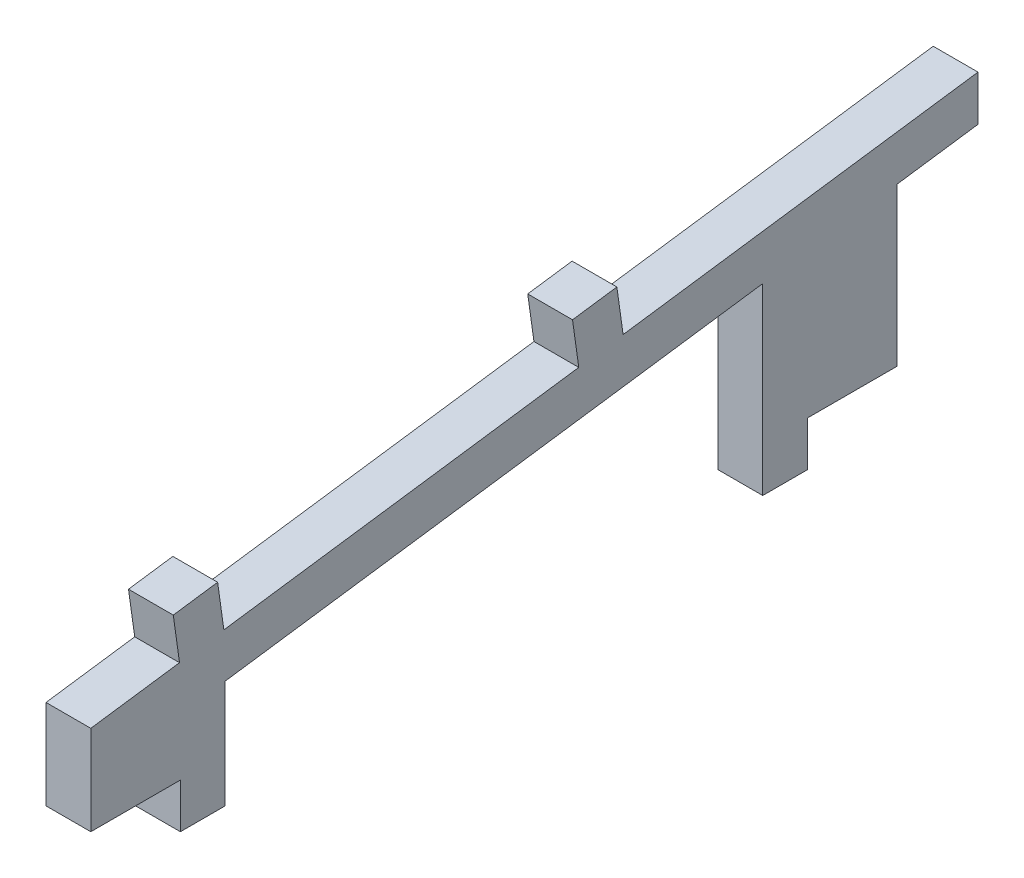
SolidWorks part; units mm, degrees
ref_plane "Front Plane" through (0, 0, 0) normal (0, 0, 1) x (1, 0, 0)
ref_plane "Top Plane" through (0, 0, 0) normal (0, 1, 0) x (1, 0, 0)
ref_plane "Right Plane" through (0, 0, 0) normal (1, 0, 0) x (0, 0, -1)
sketch "Sketch1" plane through (0, 0, 0) normal (1, 0, 0) x (0, 0, -1)
  line L0 (0, 0) -> (0, 10)
  line L1 (99.0268, 18.8682) -> (90, 17.5995)
  line L2 (99.0268, 23.9173) -> (99.0268, 18.8682)
  line L3 (90, 17.5995) -> (90, 0)
  line L4 (0, 0) -> (10, 0)
  line L5 (15, 7.059) -> (15, -5)
  line L6 (10, 0) -> (10, -5)
  line L7 (75, -5) -> (75, 15.4914)
  line L8 (75, 15.4914) -> (15, 7.059)
  line L9 (10, -5) -> (15, -5)
  line L10 (75, -5) -> (80, -5)
  line L11 (80, -5) -> (80, 0)
  line L12 (80, 0) -> (90, 0)
  line L13 (14.854, 12.0876) -> (54.4647, 17.6545)
  line L14 (0, 10) -> (9.9027, 11.3917)
  line L15 (9.9027, 11.3917) -> (9.2068, 16.3431)
  line L16 (9.2068, 16.3431) -> (14.1582, 17.0389)
  line L17 (14.1582, 17.0389) -> (14.854, 12.0876)
  line L18 (54.4647, 17.6545) -> (53.7689, 22.6059)
  line L19 (53.7689, 22.6059) -> (58.7202, 23.3017)
  line L20 (58.7202, 23.3017) -> (59.4161, 18.3504)
  line L21 (59.4161, 18.3504) -> (99.0268, 23.9173)
  dimension "D8" = 60
  dimension "D9" = 8
  dimension "D10" = 100
  dimension "D1" = 5
  dimension "D2" = 15
  dimension "D3" = 5
  dimension "D4" = 10
  dimension "D5" = 40
  dimension "D6" = 10
  dimension "D7" = 15
extrude "Boss-Extrude1" add sketch "Sketch1" along normal blind 5
equation "\"ˇ3\"=3.9176"
